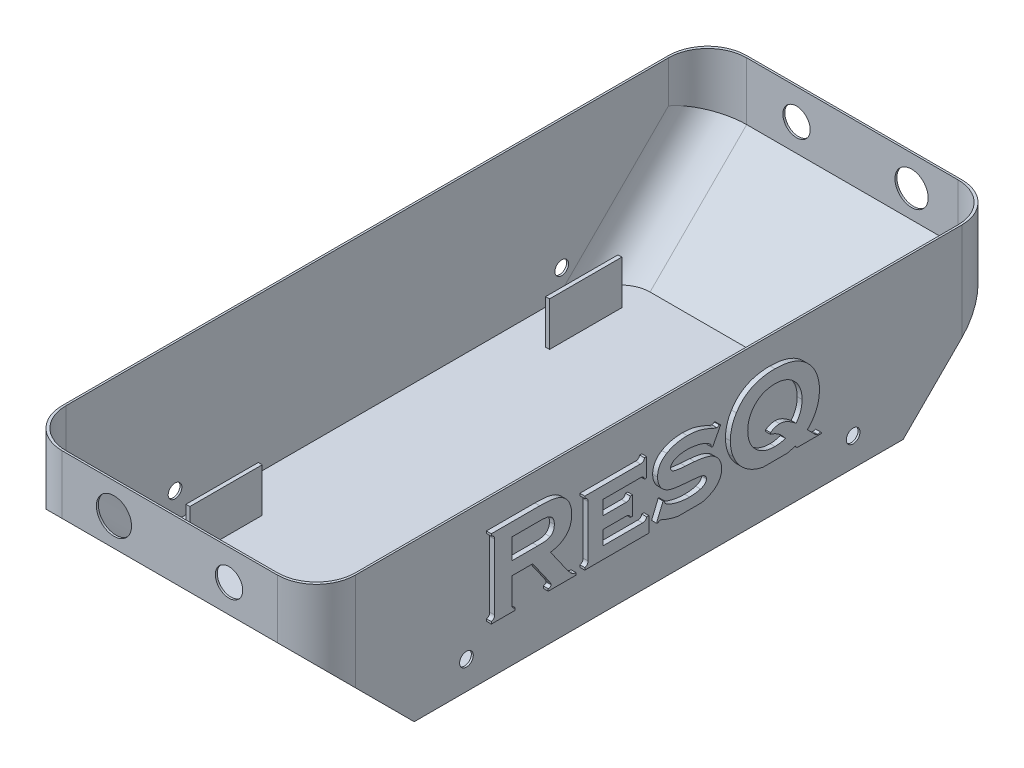
SolidWorks part; units mm, degrees
ref_plane "Front Plane" through (0, 0, 0) normal (0, 0, 1) x (1, 0, 0)
ref_plane "Top Plane" through (0, 0, 0) normal (0, 1, 0) x (1, 0, 0)
ref_plane "Right Plane" through (0, 0, 0) normal (1, 0, 0) x (0, 0, -1)
sketch "Sketch1" plane through (0, 0, 0) normal (1, 0, 0) x (0, 0, -1)
  line L3 (-115.0803, -56.5237) -> (134.9197, -56.5237)
  line L7 (-165.0803, -6.5237) -> (-115.0803, -56.5237)
  line L9 (-165.0803, -6.5237) -> (-165.0803, 23.4763)
  line L10 (-165.0803, 23.4763) -> (184.9197, 23.4763)
  line L11 (184.9197, -6.5237) -> (184.9197, 23.4763)
  line L12 (134.9197, -56.5237) -> (184.9197, -6.5237)
  dimension "D5" = 30
extrude "Boss-Extrude1" add sketch "Sketch1" along normal blind 150
shell "Shell2" thickness 1
sketch "Sketch10" plane through (150, 0, 0) normal (1, 0, 0) x (0, 0, -1)
  circle A0 centre (109.3556, -42.1811) radius 3.5
  circle A1 centre (-88.3673, -42.1811) radius 3.5
  dimension "D3" = 7
  dimension "D4" = 7
extrude "Cut-Extrude1" cut sketch "Sketch10" against normal through all
fillet "Fillet8" radius 20 6 edges at (1, -30.8166, 139.3732) (1, 8.6834, 164.0803) (149, 8.6834, 164.0803) (149, -30.8166, 139.3732) (150, 8.4763, 165.0803) (0, 8.4763, 165.0803)
fillet "Fillet10" radius 20 6 edges at (1, 8.6834, -183.9197) (1, -30.8166, -159.2125) (149, -30.8166, -159.2125) (149, 8.6834, -183.9197) (150, 8.4763, -184.9197) (0, 8.4763, -184.9197)
sketch "Sketch11" plane through (149, 0, 0) normal (-1, 0, 0) x (0, 0, 1)
  line L0 (88.3673, -42.1811) -> (100.3673, -42.1811)
  line L1 (114.6661, -55.5237) -> (86.3819, -55.5237) construction
  line L2 (100.524, -55.5237) -> (63.524, -55.5237)
  line L3 (100.524, -55.5237) -> (100.524, -33.1237)
  line L4 (100.524, -33.1237) -> (63.524, -33.1237)
  line L5 (63.524, -55.5237) -> (63.524, -33.1237)
  line L6 (-120.3633, -33.1237) -> (-120.3633, -55.5237)
  line L7 (-120.3633, -55.5237) -> (-83.3633, -55.5237)
  line L8 (-83.3633, -55.5237) -> (-83.3633, -33.1237)
  line L9 (-120.3633, -55.5237) -> (-120.3633, -33.1237)
  line L10 (-120.3633, -33.1237) -> (-83.3633, -33.1237)
  line L11 (-83.3633, -55.5237) -> (-83.3633, -33.1237)
  line L12 (63.524, -33.1237) -> (63.524, -55.5237)
  line L13 (100.524, -55.5237) -> (100.524, -33.1237)
  line L14 (100.524, -33.1237) -> (63.524, -33.1237)
  line L15 (63.524, -55.5237) -> (100.524, -55.5237)
  dimension "D1" = 12
  dimension "D2" = 37
  dimension "D3" = 22.4
sketch "Sketch12" plane through (0, 0, 0) normal (-1, 0, 0) x (0, 0, 1)
  line L0 (-83.3633, -33.1237) -> (-120.3633, -33.1237)
  line L1 (-120.3633, -33.1237) -> (-120.3633, -55.5237)
  line L2 (-120.3633, -55.5237) -> (-83.3633, -55.5237)
  line L3 (-83.3633, -55.5237) -> (-83.3633, -33.1237)
  line L4 (100.524, -33.1237) -> (63.524, -33.1237)
  line L5 (63.524, -33.1237) -> (63.524, -55.5237)
  line L6 (63.524, -55.5237) -> (100.524, -55.5237)
  line L7 (100.524, -55.5237) -> (100.524, -33.1237)
extrude "Boss-Extrude2" add sketch "Sketch12" against normal blind 2 from offset 18.74 offset against normal yes
extrude "Boss-Extrude3" add sketch "Sketch11" along normal blind 2 from offset 18.64
sketch "Sketch16" plane through (0, 0, 165.0803) normal (0, 0, 1) x (1, 0, 0)
  circle A0 centre (46.4871, 7.8362) radius 9
  circle A1 centre (105.3059, 7.8362) radius 7
  dimension "D1" = 18
  dimension "D2" = 14
extrude "Cut-Extrude2" cut sketch "Sketch16" against normal up to next
sketch "Sketch17" plane through (0, 0, -184.9197) normal (0, 0, -1) x (-1, 0, 0)
  circle A1 centre (-105.3059, 7.8362) radius 8.5
  circle A2 centre (-46.4871, 7.8362) radius 7
  dimension "D1" = 17
  dimension "D2" = 14
extrude "Cut-Extrude3" cut sketch "Sketch17" against normal up to next
sketch "Sketch19" plane through (150, 0, 0) normal (1, 0, 0) x (0, 0, -1)
  line L0 (-82.0428, -30.4869) -> (100.6766, -30.4869)
  line L1 (-67.5984, -14.3758) -> (-67.5984, -27.3185)
  line L2 (-65.9317, -29.3758) -> (-65.9317, -30.4869)
  line L3 (-65.9317, -30.4869) -> (-78.1539, -30.4869)
  line L4 (-78.1539, -30.4869) -> (-78.1539, -29.3758)
  line L5 (-76.4873, -27.2838) -> (-76.4873, 6.2839)
  line L6 (-78.1539, 8.402) -> (-78.1539, 9.5131)
  line L7 (-78.1539, 9.5131) -> (-53.3623, 9.5131)
  line L8 (-47.8849, -13.8203) -> (-40.1418, -24.8359)
  line L9 (-34.8206, -29.3758) -> (-34.8206, -30.4869)
  line L10 (-34.8206, -30.4869) -> (-49.048, -30.4869)
  line L11 (-49.048, -30.4869) -> (-49.048, -29.3758)
  line L12 (-48.9265, -25.8602) -> (-56.9994, -14.3758)
  line L13 (-56.9994, -14.3758) -> (-67.5984, -14.3758)
  line L14 (-67.5984, -7.7092) -> (-54.43, -7.7092)
  line L15 (-54.43, 2.8464) -> (-67.5984, 2.8464)
  line L16 (-67.5984, 2.8464) -> (-67.5984, -7.7092)
  line L17 (-20.9317, -17.1536) -> (-20.9317, -24.3758)
  line L18 (-20.9317, -24.3758) -> (-0.8015, -24.3758)
  line L19 (1.2905, -22.7092) -> (2.4016, -22.7092)
  line L20 (2.4016, -22.7092) -> (2.4016, -32.1536)
  line L21 (2.4016, -32.1536) -> (1.2905, -32.1536)
  line L22 (-0.8102, -30.4869) -> (-30.3762, -30.4869)
  line L23 (-30.3762, -30.4869) -> (-30.3762, -29.3758)
  line L24 (-28.7095, -27.2491) -> (-28.7095, -0.947)
  line L25 (-30.3762, 1.1797) -> (-30.3762, 2.2908)
  line L26 (-30.3762, 2.2908) -> (-1.93, 2.2908)
  line L27 (0.1794, 3.9575) -> (1.2905, 3.9575)
  line L28 (1.2905, 3.9575) -> (1.2905, -5.4869)
  line L29 (1.2905, -5.4869) -> (0.1794, -5.4869)
  line L30 (-1.9213, -3.8203) -> (-20.9317, -3.8203)
  line L31 (-20.9317, -3.8203) -> (-20.9317, -11.0425)
  line L32 (-20.9317, -11.0425) -> (-9.1349, -11.0425)
  line L33 (-7.0428, -9.3758) -> (-5.9317, -9.3758)
  line L34 (-5.9317, -9.3758) -> (-5.9317, -18.8203)
  line L35 (-5.9317, -18.8203) -> (-7.0428, -18.8203)
  line L36 (-9.1349, -17.1536) -> (-20.9317, -17.1536)
  line L37 (39.0683, -0.8949) -> (35.0231, -8.6032)
  line L38 (35.0231, -8.6032) -> (34.3026, -8.2213)
  line L39 (21.0735, -10.1571) -> (25.7957, -10.4956)
  line L40 (7.0283, -28.3342) -> (6.2905, -28.0303)
  line L41 (6.2905, -28.0303) -> (9.6672, -19.9227)
  line L42 (9.6672, -19.9227) -> (10.4051, -20.2092)
  line L43 (24.6325, -18.0217) -> (20.0058, -17.6397)
  line L44 (38.3565, -0.513) -> (39.0683, -0.8949)
  line L45 (83.4433, -25.2265) -> (86.5249, -28.3428)
  line L46 (90.1273, -29.5321) -> (90.7349, -30.2092)
  line L47 (90.7349, -30.2092) -> (82.6794, -38.2647)
  line L48 (82.6794, -38.2647) -> (81.9849, -37.5529)
  line L49 (80.8565, -33.5772) -> (77.1412, -29.2977)
  line L50 (64.6238, -17.8914) -> (64.6238, -17.0928)
  spline S0 degree 3 poles (-67.5984, -27.3185) (-67.5951, -27.5747) (-67.5616, -27.9435) (-67.4024, -28.3859) (-67.2353, -28.6575) (-66.994, -28.8764) (-66.5842, -29.1691) (-66.1946, -29.2863) (-65.9317, -29.3758) knots 0 0 0 0 0.26523 0.376661 0.482642 0.590292 0.710342 1 1 1 1
  spline S1 degree 3 poles (-78.1539, -29.3758) (-77.8837, -29.2826) (-77.4918, -29.1534) (-77.075, -28.8618) (-76.8402, -28.6396) (-76.6851, -28.362) (-76.5051, -27.9223) (-76.5037, -27.5389) (-76.4873, -27.2838) knots 0 0 0 0 0.294383 0.413201 0.517636 0.620979 0.735076 1 1 1 1
  spline S2 degree 3 poles (-76.4873, 6.2839) (-76.5051, 6.5446) (-76.503, 6.9341) (-76.6846, 7.3799) (-76.8429, 7.6573) (-77.0716, 7.8884) (-77.4933, 8.1781) (-77.8828, 8.3096) (-78.1539, 8.402) knots 0 0 0 0 0.268643 0.381839 0.484365 0.590067 0.707945 1 1 1 1
  spline S3 degree 3 poles (-53.3623, 9.5131) (-52.0077, 9.5065) (-50.0869, 9.469) (-47.6906, 9.2443) (-46.2162, 9.0108) (-44.9008, 8.6929) (-43.3106, 8.1651) (-42.2152, 7.5842) (-41.5394, 7.1433) knots 0 0 0 0 0.332258 0.470557 0.58988 0.697946 0.80205 1 1 1 1
  spline S4 degree 3 poles (-41.5394, 7.1433) (-40.7911, 6.6439) (-39.4164, 5.4274) (-38.4808, 3.8483) (-38.1192, 3.0113) knots 0 0 0 0 0.496545 1 1 1 1
  spline S5 degree 3 poles (-38.1192, 3.0113) (-37.763, 2.1739) (-37.2107, 0.4054) (-37.0466, -1.4397) (-37.0428, -2.3706) knots 0 0 0 0 0.494205 1 1 1 1
  spline S6 degree 3 poles (-37.0428, -2.3706) (-37.0392, -3.1464) (-37.1267, -4.2842) (-37.4039, -5.7449) (-37.7009, -6.7508) (-38.0832, -7.6938) (-38.5529, -8.5718) (-39.1039, -9.3878) (-39.742, -10.1382) (-40.4672, -10.8268) (-41.2758, -11.4518) (-42.1717, -12.0119) (-43.1516, -12.5042) (-44.2165, -12.9272) (-45.7852, -13.43) (-47.0288, -13.6828) (-47.8849, -13.8203) knots 0 0 0 0 0.132813 0.194929 0.254369 0.312172 0.368939 0.424617 0.480529 0.537325 0.595621 0.655306 0.718038 0.783203 0.85139 1 1 1 1
  spline S7 degree 3 poles (-40.1418, -24.8359) (-39.8343, -25.2722) (-39.3673, -25.8803) (-38.7804, -26.6587) (-38.3854, -27.1443) (-38.0358, -27.5752) (-37.699, -27.9256) (-37.4196, -28.2333) (-37.0846, -28.5486) (-36.6516, -28.8522) (-35.8883, -29.2213) (-35.2536, -29.3543) (-34.8206, -29.3758) knots 0 0 0 0 0.220518 0.316906 0.402813 0.479214 0.546062 0.603586 0.650968 0.735905 0.820942 1 1 1 1
  spline S8 degree 3 poles (-49.048, -29.3758) (-48.6789, -29.2978) (-47.9752, -29.1987) (-47.5651, -28.6164) (-47.5724, -28.3428) knots 0 0 0 0 0.603053 1 1 1 1
  spline S9 degree 3 poles (-47.5724, -28.3428) (-47.6152, -28.0265) (-48.0444, -27.1701) (-48.5716, -26.3873) (-48.9265, -25.8602) knots 0 0 0 0 0.33191 1 1 1 1
  spline S10 degree 3 poles (-54.43, -7.7092) (-53.5993, -7.7151) (-52.4615, -7.6942) (-51.0892, -7.6263) (-49.7741, -7.492) (-48.7929, -7.1752) (-48.1105, -6.7977) knots 0 0 0 0 0.386033 0.528806 0.638402 1 1 1 1
  spline S11 degree 3 poles (-48.1105, -6.7977) (-47.7528, -6.6106) (-47.28, -6.2364) (-46.7639, -5.6229) (-46.4664, -5.0951) (-46.2147, -4.5191) (-45.9964, -3.6275) (-45.9285, -2.9211) (-45.9317, -2.4314) knots 0 0 0 0 0.234599 0.348598 0.465953 0.587078 0.714519 1 1 1 1
  spline S12 degree 3 poles (-45.9317, -2.4314) (-45.9285, -1.9417) (-45.9964, -1.2353) (-46.2147, -0.3437) (-46.4664, 0.2324) (-46.7639, 0.7601) (-47.28, 1.3736) (-47.7528, 1.7479) (-48.1105, 1.9349) knots 0 0 0 0 0.285481 0.412922 0.534047 0.651402 0.765401 1 1 1 1
  spline S13 degree 3 poles (-48.1105, 1.9349) (-48.7765, 2.3394) (-49.7569, 2.6456) (-51.0637, 2.7605) (-52.4409, 2.8358) (-53.5879, 2.8496) (-54.43, 2.8464) knots 0 0 0 0 0.359612 0.467633 0.608938 1 1 1 1
  spline S14 degree 3 poles (-0.8015, -24.3758) (-0.5438, -24.3653) (-0.1684, -24.3481) (0.2777, -24.1917) (0.5463, -24.025) (0.7801, -23.7999) (1.0607, -23.3682) (1.2013, -22.9827) (1.2905, -22.7092) knots 0 0 0 0 0.264663 0.377612 0.478334 0.584774 0.705907 1 1 1 1
  spline S15 degree 3 poles (1.2905, -32.1536) (1.2207, -31.8814) (1.0777, -31.5058) (0.7951, -31.0877) (0.5604, -30.8616) (0.2869, -30.6883) (-0.1669, -30.5215) (-0.5485, -30.4919) (-0.8102, -30.4869) knots 0 0 0 0 0.286301 0.404825 0.511106 0.615741 0.732307 1 1 1 1
  spline S16 degree 3 poles (-30.3762, -29.3758) (-30.1065, -29.2959) (-29.7287, -29.1554) (-29.3106, -28.8714) (-29.0812, -28.6361) (-28.9135, -28.3561) (-28.7417, -27.8992) (-28.7148, -27.5131) (-28.7095, -27.2491) knots 0 0 0 0 0.28542 0.403192 0.508799 0.615255 0.731083 1 1 1 1
  spline S17 degree 3 poles (-28.7095, -0.947) (-28.7316, -0.6876) (-28.7207, -0.2976) (-28.9096, 0.1418) (-29.0619, 0.4179) (-29.2996, 0.6394) (-29.7109, 0.9446) (-30.1061, 1.0806) (-30.3762, 1.1797) knots 0 0 0 0 0.268839 0.379402 0.482015 0.585712 0.705392 1 1 1 1
  spline S18 degree 3 poles (-1.93, 2.2908) (-1.6651, 2.2937) (-1.2851, 2.3268) (-0.8319, 2.4857) (-0.5572, 2.6474) (-0.3223, 2.8757) (-0.0451, 3.3045) (0.1048, 3.6823) (0.1794, 3.9575) knots 0 0 0 0 0.269618 0.381976 0.484678 0.59056 0.71106 1 1 1 1
  spline S19 degree 3 poles (0.1794, -5.4869) (0.097, -5.2133) (-0.0366, -4.8255) (-0.3254, -4.4046) (-0.5566, -4.1756) (-0.8319, -4.0198) (-1.2724, -3.832) (-1.6616, -3.8421) (-1.9213, -3.8203) knots 0 0 0 0 0.292176 0.410496 0.516593 0.619503 0.730385 1 1 1 1
  spline S20 degree 3 poles (-9.1349, -11.0425) (-8.8784, -11.0393) (-8.5103, -11.0054) (-8.0707, -10.8481) (-7.8045, -10.683) (-7.57, -10.4581) (-7.294, -10.0245) (-7.129, -9.6516) (-7.0428, -9.3758) knots 0 0 0 0 0.263699 0.374486 0.475766 0.582794 0.704597 1 1 1 1
  spline S21 degree 3 poles (-7.0428, -18.8203) (-7.1206, -18.5493) (-7.2677, -18.1727) (-7.5446, -17.75) (-7.7735, -17.5172) (-8.041, -17.3493) (-8.4922, -17.187) (-8.8706, -17.16) (-9.1349, -17.1536) knots 0 0 0 0 0.28793 0.409173 0.5136 0.618485 0.728763 1 1 1 1
  spline S22 degree 3 poles (34.3026, -8.2213) (34.3145, -7.9243) (34.208, -7.3547) (33.891, -6.8678) (33.6776, -6.6935) knots 0 0 0 0 0.521001 1 1 1 1
  spline S23 degree 3 poles (33.6776, -6.6935) (33.0396, -6.1457) (31.8992, -5.4381) (30.1622, -4.7091) (28.6232, -4.214) (26.9838, -3.7914) (24.7389, -3.3878) (23.0335, -3.264) (21.8981, -3.2647) knots 0 0 0 0 0.201656 0.320398 0.452166 0.590008 0.727138 1 1 1 1
  spline S24 degree 3 poles (21.8981, -3.2647) (20.9851, -3.2762) (19.2377, -3.3638) (17.5347, -3.7696) (16.7506, -4.0373) knots 0 0 0 0 0.52465 1 1 1 1
  spline S25 degree 3 poles (16.7506, -4.0373) (16.2688, -4.2139) (15.578, -4.4823) (14.7903, -4.9881) (14.3202, -5.3673) (13.9556, -5.7893) (13.6128, -6.3977) (13.5143, -6.9111) (13.5127, -7.2491) knots 0 0 0 0 0.316406 0.451562 0.574052 0.686304 0.792178 1 1 1 1
  spline S26 degree 3 poles (13.5127, -7.2491) (13.4892, -7.6792) (13.7209, -8.3236) (14.3962, -8.937) (14.9681, -9.2071) (15.5266, -9.3769) (16.0484, -9.5213) (16.6685, -9.6338) (17.3738, -9.7571) (18.1699, -9.8698) (19.411, -10.0104) (20.3886, -10.1152) (21.0735, -10.1571) knots 0 0 0 0 0.144782 0.220299 0.306475 0.358353 0.419716 0.491228 0.573432 0.664269 0.765759 1 1 1 1
  spline S27 degree 3 poles (25.7957, -10.4956) (26.7689, -10.5651) (28.1785, -10.7264) (29.9921, -11.0168) (31.2143, -11.2862) (32.3477, -11.598) (33.6929, -12.0535) (34.6315, -12.4821) (35.2054, -12.8133) knots 0 0 0 0 0.299637 0.435686 0.564012 0.683916 0.796636 1 1 1 1
  spline S28 degree 3 poles (35.2054, -12.8133) (35.7976, -13.1492) (36.8892, -13.9785) (37.7836, -15.0177) (38.1568, -15.5911) knots 0 0 0 0 0.498731 1 1 1 1
  spline S29 degree 3 poles (38.1568, -15.5911) (38.6351, -16.2996) (39.4011, -17.8737) (39.6164, -19.6098) (39.6238, -20.4782) knots 0 0 0 0 0.495739 1 1 1 1
  spline S30 degree 3 poles (39.6238, -20.4782) (39.6312, -21.2677) (39.489, -22.4362) (39.0078, -23.9049) (38.5049, -24.9223) (37.8681, -25.8784) (36.7822, -27.0804) (35.8038, -27.8482) (35.0839, -28.2907) knots 0 0 0 0 0.249932 0.369677 0.48818 0.608461 0.732496 1 1 1 1
  spline S31 degree 3 poles (35.0839, -28.2907) (34.3301, -28.7519) (33.1251, -29.3856) (31.3797, -29.985) (29.9591, -30.3847) (28.4357, -30.6692) (26.2255, -30.9693) (24.5095, -31.0414) (23.3391, -31.0425) knots 0 0 0 0 0.217184 0.332447 0.452575 0.579221 0.712545 1 1 1 1
  spline S32 degree 3 poles (23.3391, -31.0425) (22.1043, -31.0382) (20.2527, -30.944) (17.8092, -30.6101) (15.9969, -30.2483) (14.1983, -29.8012) (11.8113, -29.0485) (10.055, -28.3604) (8.912, -27.822) knots 0 0 0 0 0.248652 0.372746 0.496268 0.620623 0.745751 1 1 1 1
  spline S33 degree 2 poles (8.912, -27.822) (8.537, -27.6382) (8.1221, -27.6137) knots 0 0 0 1 1 1
  spline S34 degree 3 poles (8.1221, -27.6137) (7.9171, -27.6067) (7.4822, -27.7828) (7.176, -28.131) (7.0283, -28.3342) knots 0 0 0 0 0.441947 1 1 1 1
  spline S35 degree 2 poles (10.4051, -20.2092) (10.4051, -20.3263) (10.4051, -20.4435) knots 0 0 0 1 1 1
  spline S36 degree 3 poles (10.4051, -20.4435) (10.3981, -20.686) (10.5086, -21.1719) (10.8027, -21.5733) (10.9867, -21.7369) knots 0 0 0 0 0.495352 1 1 1 1
  spline S37 degree 3 poles (10.9867, -21.7369) (11.2599, -21.9663) (11.7159, -22.2973) (12.4054, -22.6729) (13.0167, -22.9445) (13.6836, -23.2238) (14.4171, -23.4969) (15.2225, -23.7416) (16.3749, -24.066) (17.8587, -24.4121) (20.2348, -24.798) (22.0239, -24.9361) (23.2089, -24.9314) knots 0 0 0 0 0.083509 0.131395 0.183518 0.239988 0.300624 0.366595 0.436921 0.580824 0.722886 1 1 1 1
  spline S38 degree 3 poles (23.2089, -24.9314) (24.1942, -24.92) (26.0838, -24.8322) (27.9318, -24.424) (28.7905, -24.1588) knots 0 0 0 0 0.523254 1 1 1 1
  spline S39 degree 3 poles (28.7905, -24.1588) (29.2506, -24.0195) (29.8981, -23.7732) (30.6497, -23.3167) (31.0789, -22.9441) (31.4338, -22.5545) (31.7486, -21.9546) (31.8571, -21.4583) (31.8461, -21.1206) knots 0 0 0 0 0.310813 0.445202 0.565882 0.677235 0.783493 1 1 1 1
  spline S40 degree 3 poles (31.8461, -21.1206) (31.8436, -20.856) (31.7857, -20.4607) (31.564, -19.9841) (31.3184, -19.6764) (31.0184, -19.3946) (30.507, -19.04) (30.0435, -18.8785) (29.728, -18.7682) knots 0 0 0 0 0.232385 0.344785 0.456984 0.575494 0.705042 1 1 1 1
  spline S41 degree 3 poles (29.728, -18.7682) (29.4493, -18.6778) (28.9899, -18.5662) (28.3255, -18.4506) (27.7237, -18.3545) (27.0526, -18.2593) (26.0145, -18.1375) (25.1996, -18.0733) (24.6325, -18.0217) knots 0 0 0 0 0.170276 0.274587 0.392172 0.524735 0.668766 1 1 1 1
  spline S42 degree 3 poles (20.0058, -17.6397) (18.9076, -17.5484) (17.3656, -17.4132) (15.4632, -17.1329) (14.3356, -16.9056) (13.3475, -16.6415) (12.1798, -16.2177) (11.3541, -15.8267) (10.8478, -15.513) knots 0 0 0 0 0.348445 0.489066 0.607646 0.711941 0.812053 1 1 1 1
  spline S43 degree 3 poles (10.8478, -15.513) (10.2318, -15.1299) (9.3805, -14.4323) (8.4621, -13.2889) (7.8816, -12.3346) (7.4245, -11.3036) (6.9766, -9.8445) (6.8476, -8.6966) (6.8461, -7.9262) knots 0 0 0 0 0.242961 0.36499 0.489852 0.616139 0.741867 1 1 1 1
  spline S44 degree 3 poles (6.8461, -7.9262) (6.8342, -7.0758) (6.983, -5.8236) (7.4774, -4.25) (7.9914, -3.1718) (8.6653, -2.1837) (9.7562, -0.9258) (10.7949, -0.1761) (11.5249, 0.277) knots 0 0 0 0 0.257037 0.378312 0.497746 0.616971 0.739193 1 1 1 1
  spline S45 degree 3 poles (11.5249, 0.277) (12.2501, 0.7021) (13.3871, 1.2919) (15.0142, 1.8536) (16.301, 2.2272) (17.6587, 2.4942) (19.5806, 2.7898) (21.0676, 2.8299) (22.0717, 2.8464) knots 0 0 0 0 0.229786 0.347964 0.469493 0.595291 0.72544 1 1 1 1
  spline S46 degree 3 poles (22.0717, 2.8464) (23.1717, 2.8589) (24.7935, 2.7516) (26.9088, 2.4436) (28.444, 2.0919) (30.0263, 1.6275) (32.3957, 0.782) (34.2066, -0.0185) (35.4572, -0.5998) knots 0 0 0 0 0.236335 0.348968 0.459309 0.574689 0.703389 1 1 1 1
  spline S47 degree 3 poles (35.4572, -0.5998) (35.8007, -0.7431) (36.3384, -1.001) (36.9175, -1.1546) (37.1412, -1.164) knots 0 0 0 0 0.626022 1 1 1 1
  spline S48 degree 3 poles (37.1412, -1.164) (37.3343, -1.1539) (37.7838, -0.9951) (38.1464, -0.6892) (38.3565, -0.513) knots 0 0 0 0 0.409769 1 1 1 1
  spline S49 degree 3 poles (86.5249, -28.3428) (86.8054, -28.6437) (87.2017, -29.0239) (87.6706, -29.4637) (88.0847, -29.8014) (88.4946, -29.8953) (88.7905, -29.8967) knots 0 0 0 0 0.436044 0.581518 0.682141 1 1 1 1
  spline S50 degree 3 poles (88.7905, -29.8967) (88.9735, -29.8884) (89.4283, -29.7896) (89.864, -29.63) (90.1273, -29.5321) knots 0 0 0 0 0.393747 1 1 1 1
  spline S51 degree 3 poles (81.9849, -37.5529) (82.1571, -37.2751) (82.446, -36.8196) (82.6047, -36.3025) (82.6186, -36.0946) knots 0 0 0 0 0.612972 1 1 1 1
  spline S52 degree 3 poles (82.6186, -36.0946) (82.6166, -35.9661) (82.5252, -35.7639) (82.3568, -35.474) (82.166, -35.1808) (81.922, -34.8404) (81.4832, -34.2975) (81.1204, -33.8726) (80.8565, -33.5772) knots 0 0 0 0 0.1213 0.211584 0.324957 0.459366 0.616765 1 1 1 1
  spline S53 degree 3 poles (77.1412, -29.2977) (76.4012, -29.5941) (75.2494, -29.987) (73.6455, -30.3675) (72.3701, -30.6238) (71.0311, -30.8134) (69.1325, -30.9814) (67.678, -31.0522) (66.6898, -31.0425) knots 0 0 0 0 0.224382 0.341699 0.463709 0.590386 0.722057 1 1 1 1
  spline S54 degree 3 poles (66.6898, -31.0425) (65.0797, -31.0386) (62.7105, -30.8963) (59.6756, -30.29) (57.5761, -29.6763) (55.6033, -28.8853) (53.1518, -27.5955) (51.4842, -26.3648) (50.4832, -25.4262) knots 0 0 0 0 0.275133 0.403624 0.527762 0.648141 0.765943 1 1 1 1
  spline S55 degree 3 poles (50.4832, -25.4262) (49.4035, -24.4449) (47.4904, -22.2033) (46.0916, -19.6099) (45.5526, -18.2387) knots 0 0 0 0 0.497481 1 1 1 1
  spline S56 degree 3 poles (45.5526, -18.2387) (45.0544, -17.019) (44.3136, -14.4586) (44.0706, -11.8052) (44.0683, -10.4696) knots 0 0 0 0 0.496436 1 1 1 1
  spline S57 degree 3 poles (44.0683, -10.4696) (44.0798, -9.4957) (44.1538, -8.0424) (44.4869, -6.1454) (44.822, -4.7665) (45.2606, -3.4215) (45.9712, -1.664) (46.6391, -0.3999) (47.1499, 0.4072) knots 0 0 0 0 0.255269 0.379846 0.5039 0.626591 0.749996 1 1 1 1
  spline S58 degree 3 poles (47.1499, 0.4072) (47.6452, 1.1906) (48.4322, 2.3314) (49.6554, 3.6929) (50.6084, 4.6487) (51.6356, 5.5124) (52.7183, 6.31) (53.8628, 7.0269) (55.0671, 7.6754) (56.3341, 8.2362) (57.6603, 8.7221) (59.0443, 9.1431) (60.493, 9.4747) (61.9986, 9.7476) (64.1244, 10.0041) (65.7567, 10.071) (66.8634, 10.0686) knots 0 0 0 0 0.12091 0.179937 0.238329 0.296652 0.354649 0.413444 0.472489 0.532751 0.593832 0.656459 0.721124 0.787396 0.855774 1 1 1 1
  spline S59 degree 3 poles (66.8634, 10.0686) (68.4966, 10.0643) (70.8974, 9.9231) (73.9703, 9.3173) (76.0895, 8.7022) (78.0777, 7.9132) (80.5394, 6.6251) (82.2073, 5.39) (83.2089, 4.4523) knots 0 0 0 0 0.276942 0.405894 0.530025 0.650395 0.76773 1 1 1 1
  spline S60 degree 3 poles (83.2089, 4.4523) (84.2843, 3.4704) (86.201, 1.2417) (87.6002, -1.3437) (88.1395, -2.7092) knots 0 0 0 0 0.497954 1 1 1 1
  spline S61 degree 3 poles (88.1395, -2.7092) (88.6377, -3.9288) (89.3785, -6.4892) (89.6215, -9.1426) (89.6238, -10.4782) knots 0 0 0 0 0.496436 1 1 1 1
  spline S62 degree 3 poles (89.6238, -10.4782) (89.6207, -11.885) (89.4536, -13.9753) (88.7894, -16.6533) (88.1147, -18.5524) (87.2356, -20.3618) (85.8067, -22.6931) (84.4341, -24.2526) (83.4433, -25.2265) knots 0 0 0 0 0.25674 0.380118 0.502297 0.623609 0.746334 1 1 1 1
  spline S63 degree 3 poles (77.6707, -19.4887) (78.1761, -18.8593) (78.8386, -17.8489) (79.553, -16.4139) (79.9897, -15.3023) (80.316, -14.1465) (80.6527, -12.5381) (80.7227, -11.2901) (80.7349, -10.4522) knots 0 0 0 0 0.248718 0.371232 0.493855 0.616427 0.741204 1 1 1 1
  spline S64 degree 3 poles (80.7349, -10.4522) (80.7365, -9.4227) (80.6085, -7.9019) (80.1384, -5.9593) (79.6504, -4.6053) (79.0209, -3.3256) (77.9788, -1.7146) (76.9997, -0.6419) (76.2818, 0.0079) knots 0 0 0 0 0.263375 0.388318 0.510298 0.630785 0.752325 1 1 1 1
  spline S65 degree 3 poles (76.2818, 0.0079) (75.6727, 0.5697) (74.6729, 1.3117) (73.2145, 2.0935) (72.063, 2.5726) (70.8507, 2.9455) (69.1222, 3.3144) (67.7744, 3.3976) (66.8634, 3.402) knots 0 0 0 0 0.242333 0.362429 0.483522 0.606731 0.733121 1 1 1 1
  spline S66 degree 3 poles (66.8634, 3.402) (65.9465, 3.398) (64.5906, 3.3136) (62.8525, 2.9471) (61.6358, 2.5705) (60.4795, 2.0958) (59.0195, 1.311) (58.0193, 0.5701) (57.4103, 0.0079) knots 0 0 0 0 0.267684 0.394483 0.517288 0.638762 0.758464 1 1 1 1
  spline S67 degree 3 poles (57.4103, 0.0079) (56.6902, -0.6467) (55.7182, -1.73) (54.6683, -3.3443) (54.044, -4.6296) (53.5534, -5.9851) (53.0829, -7.9308) (52.9568, -9.4546) (52.9572, -10.4869) knots 0 0 0 0 0.248155 0.369392 0.490242 0.611918 0.73655 1 1 1 1
  spline S68 degree 3 poles (52.9572, -10.4869) (52.9552, -11.5224) (53.0846, -13.0512) (53.5518, -15.0036) (54.044, -16.3616) (54.6686, -17.6467) (55.7141, -19.2589) (56.692, -20.3321) (57.4103, -20.9817) knots 0 0 0 0 0.264094 0.389397 0.51103 0.631837 0.75303 1 1 1 1
  spline S69 degree 3 poles (57.4103, -20.9817) (58.0254, -21.5439) (59.0341, -22.2859) (60.5038, -23.0674) (61.664, -23.5464) (62.8849, -23.9194) (64.6223, -24.2873) (65.9754, -24.3726) (66.8895, -24.3758) knots 0 0 0 0 0.242389 0.362587 0.483811 0.607167 0.733705 1 1 1 1
  spline S70 degree 3 poles (66.8895, -24.3758) (67.7902, -24.3704) (69.6025, -24.2254) (71.3543, -23.7396) (72.2106, -23.4383) knots 0 0 0 0 0.49804 1 1 1 1
  spline S71 degree 2 poles (72.2106, -23.4383) (71.9496, -23.0891) (71.6724, -22.7526) knots 0 0 0 1 1 1
  spline S72 degree 3 poles (71.6724, -22.7526) (71.1993, -22.1241) (70.4235, -21.2638) (69.3047, -20.2346) (68.4316, -19.5884) (67.5356, -19.0128) (66.2835, -18.396) (65.2998, -18.0449) (64.6238, -17.8914) knots 0 0 0 0 0.269822 0.397173 0.521398 0.642438 0.762438 1 1 1 1
  spline S73 degree 3 poles (64.6238, -17.0928) (65.2815, -16.5741) (66.7701, -15.7392) (68.4574, -15.4928) (69.294, -15.4869) knots 0 0 0 0 0.500078 1 1 1 1
  spline S74 degree 3 poles (69.294, -15.4869) (69.9291, -15.4781) (70.8839, -15.6066) (72.1268, -15.9792) (73.0841, -16.3799) (74.0923, -16.9296) (75.6655, -17.9265) (76.8441, -18.8377) (77.6707, -19.4887) knots 0 0 0 0 0.200734 0.303108 0.410356 0.528873 0.666459 1 1 1 1
extrude "Boss-Extrude5" add sketch "Sketch19" along normal mid plane 5 contours S9 S8 L11 L0 L9 S7 L8 S6 S5 S4 S3 L7 L6 S2 L5 S1 L4 L2 S0 L1 L13 L12 S13 S12 S11 S10 L14 L16 L15 | S21 L35 L34 L33 S20 L32 L31 L30 S19 L29 L28 L27 S18 L26 L25 S17 L24 S16 L23 L0 L20 L19 S14 L18 L17 L36 | S48 S47 S46 S45 S44 S43 S42 L43 S41 S40 S39 S38 S37 S36 S35 L42 L41 L40 S34 S33 S32 L0 S31 S30 S29 S28 S27 L39 S26 S25 S24 S23 S22 L38 L37 L44 | S62 S61 S60 S59 S58 S57 S56 S55 S54 L0 S53 L49 L47 L46 S50 S49 L45 S74 S73 L50 S72 S71 S70 S69 S68 S67 S66 S65 S64 S63
